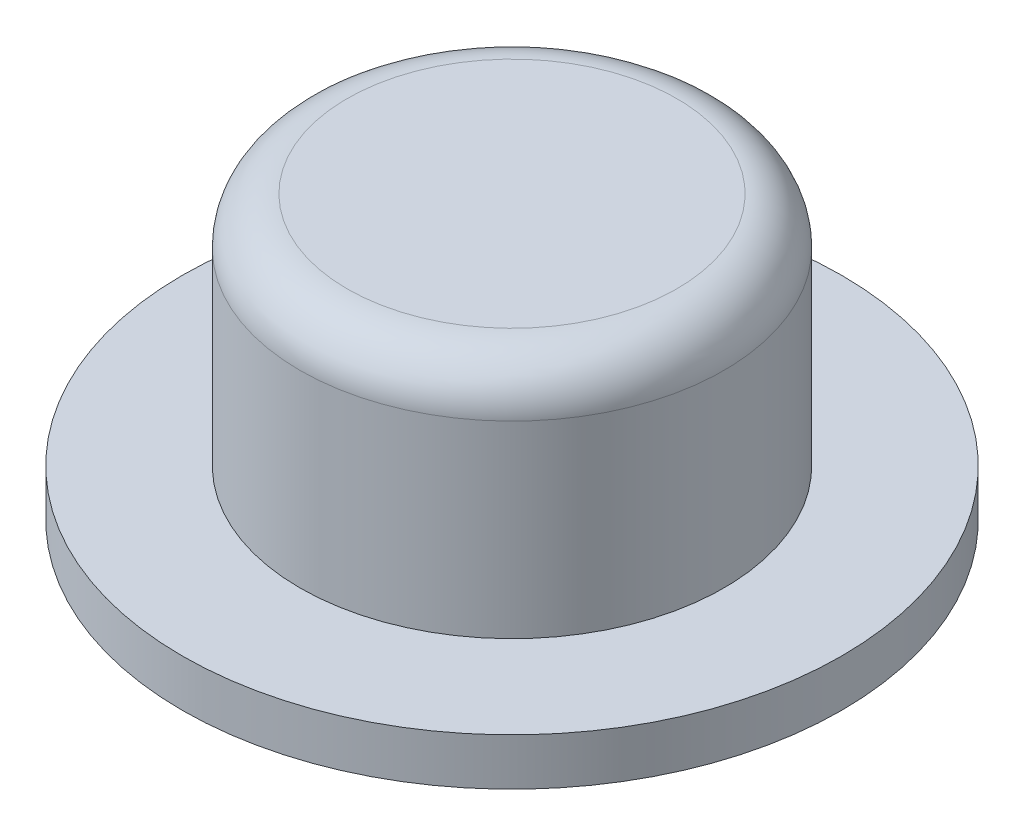
SolidWorks part; units mm, degrees
ref_plane "Front Plane" through (0, 0, 0) normal (0, 0, 1) x (1, 0, 0)
ref_plane "Top Plane" through (0, 0, 0) normal (0, 1, 0) x (1, 0, 0)
ref_plane "Right Plane" through (0, 0, 0) normal (1, 0, 0) x (0, 0, -1)
sketch "Sketch1" plane through (0, 0, 0) normal (0, 0, 1) x (1, 0, 0)
  line L0 (0, 6) -> (0, 0)
  line L1 (0, 0) -> (-7, 0)
  line L2 (-7, 0) -> (-7, 1)
  line L3 (-7, 1) -> (-4.5, 1)
  line L4 (-4.5, 1) -> (-4.5, 5)
  line L5 (-3.5, 6) -> (0, 6)
  arc A0 (-4.5, 5) -> (-3.5, 6) centre (-3.5, 5) cw
  point P9 (-4.5, 6)
  dimension "D5" = 1
  dimension "D1" = 6
  dimension "D2" = 4.5
  dimension "D3" = 7
  dimension "D4" = 1
revolve "Centre Button" add sketch "Sketch1" angle 360 about L0
